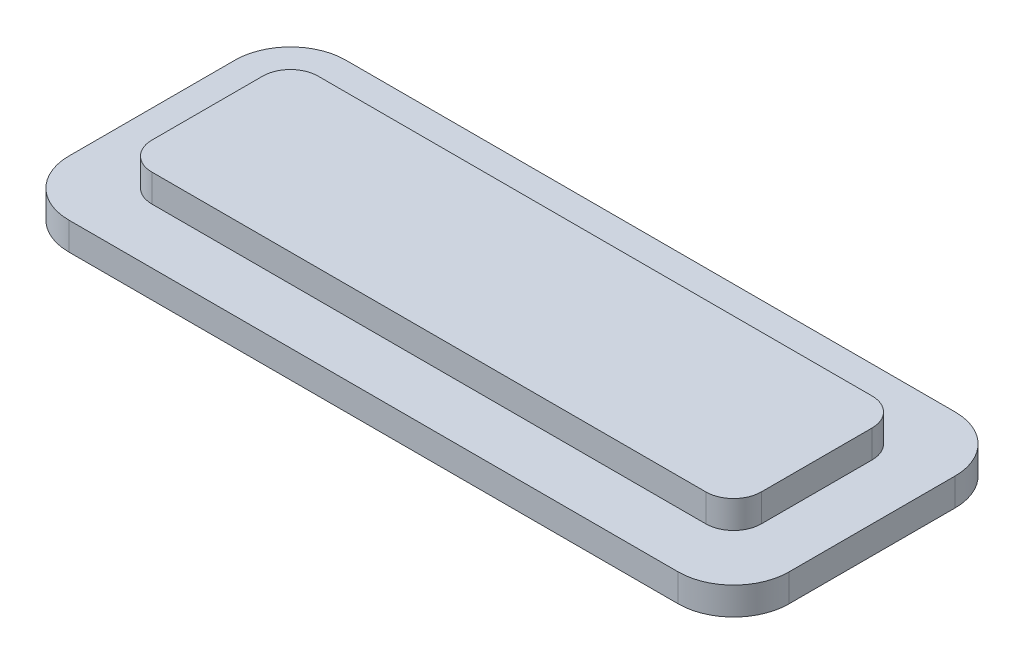
SolidWorks part; units mm, degrees
ref_plane "Front Plane" through (0, 0, 0) normal (0, 0, 1) x (1, 0, 0)
ref_plane "Top Plane" through (0, 0, 0) normal (0, 1, 0) x (1, 0, 0)
ref_plane "Right Plane" through (0, 0, 0) normal (1, 0, 0) x (0, 0, -1)
other "Configuration Table"
sketch "Sketch1" plane through (0, 0, 0) normal (0, 1, 0) x (1, 0, 0)
  line L1 (11, 3) -> (-11, 3)
  line L2 (11, 3) -> (11, -3)
  line L3 (11, -3) -> (-11, -3)
  line L4 (-11, 3) -> (-11, -3)
  line L5 (11, 3) -> (-11, -3) construction
  line L6 (11, -3) -> (-11, 3) construction
  point P0 (0, 0)
  dimension "D1" = 6
  dimension "D2" = 22
extrude "Boss-Extrude1" add sketch "Sketch1" along normal blind 1 contours L2 L1 L4 L3
sketch "Sketch2" plane through (0, 0, 0) normal (0, -1, 0) x (1, 0, 0)
  line L1 (11, 5) -> (-11, 5)
  line L2 (13, 3) -> (13, -3)
  line L3 (11, -5) -> (-11, -5)
  line L4 (-13, 3) -> (-13, -3)
  line L5 (13, 5) -> (-13, -5) construction
  line L6 (13, -5) -> (-13, 5) construction
  arc A0 (11, 5) -> (13, 3) centre (11, 3) cw
  arc A1 (13, -3) -> (11, -5) centre (11, -3) cw
  arc A2 (-11, -5) -> (-13, -3) centre (-11, -3) cw
  arc A3 (-11, 5) -> (-13, 3) centre (-11, 3) ccw
  point P0 (0, 0)
  dimension "D3" = 2
  dimension "D1" = 10
  dimension "D2" = 26
extrude "Boss-Extrude2" add sketch "Sketch2" along normal blind 1
fillet "Fillet1" radius 1 4 edges at (11, 0.5, -3) (11, 0.5, 3) (-11, 0.5, -3) (-11, 0.5, 3)
